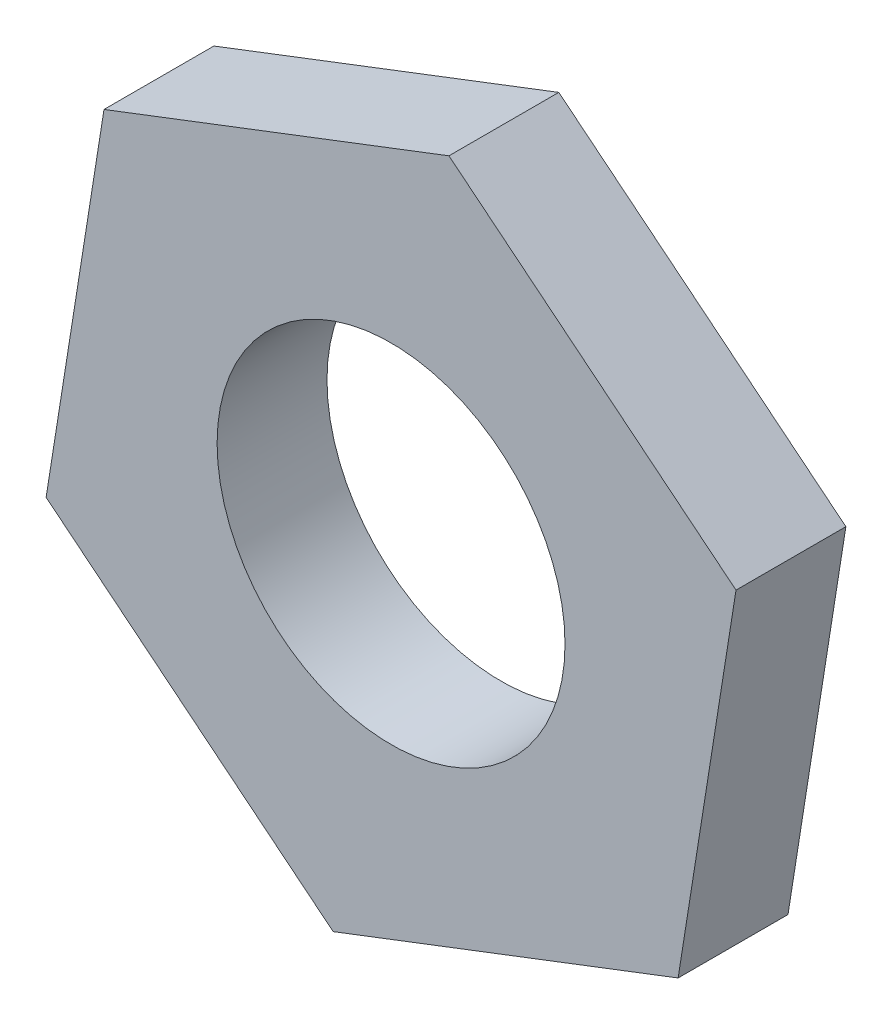
SolidWorks part; units mm, degrees
material "Hierro dúctil"
ref_plane "Alzado" through (0, 0, 0) normal (0, 0, 1) x (1, 0, 0)
ref_plane "Planta" through (0, 0, 0) normal (0, 1, 0) x (1, 0, 0)
ref_plane "Vista lateral" through (0, 0, 0) normal (1, 0, 0) x (0, 0, -1)
sketch "Croquis1" plane through (0, 0, 0) normal (0, 0, 1) x (1, 0, 0)
  line L1 (7.8379, -6.3504) -> (9.4185, 3.6127)
  line L2 (9.4185, 3.6127) -> (1.5806, 9.963)
  line L3 (1.5806, 9.963) -> (-7.8379, 6.3504)
  line L4 (-7.8379, 6.3504) -> (-9.4185, -3.6127)
  line L5 (-9.4185, -3.6127) -> (-1.5806, -9.963)
  line L6 (-1.5806, -9.963) -> (7.8379, -6.3504)
  circle A0 centre (0, 0) radius 4.75
  dimension "D1" = 9.5
extrude "Saliente-Extruir1" add sketch "Croquis1" along normal blind 3
